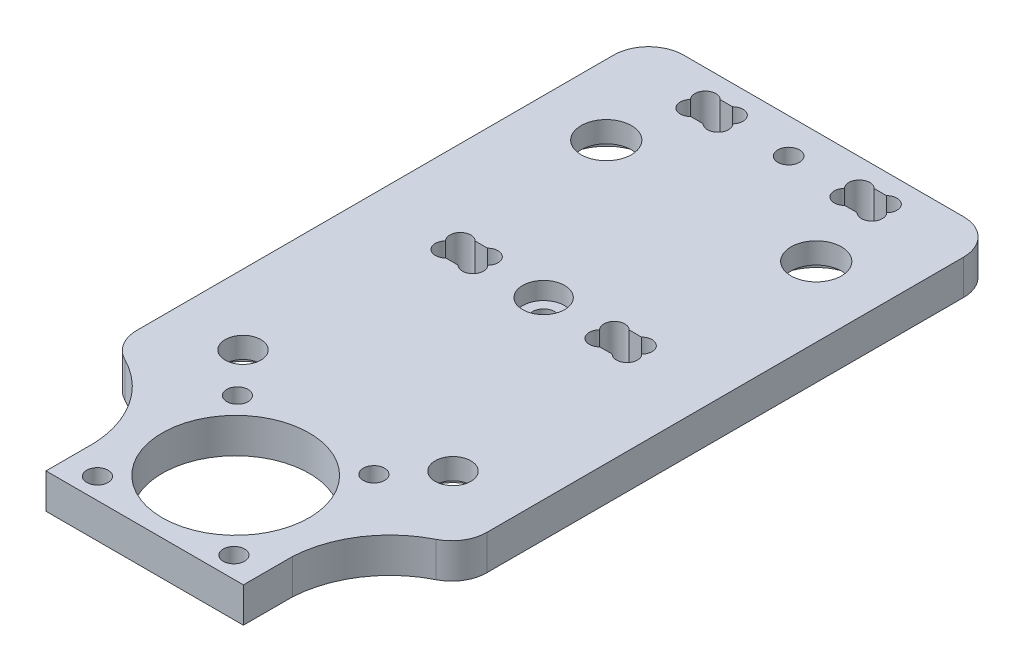
SolidWorks part; units mm, degrees
ref_plane "Alzado" through (0, 0, 0) normal (0, 0, 1) x (1, 0, 0)
ref_plane "Planta" through (0, 0, 0) normal (0, 1, 0) x (1, 0, 0)
ref_plane "Vista lateral" through (0, 0, 0) normal (1, 0, 0) x (0, 0, -1)
sketch "Croquis1" plane through (0, 0, 0) normal (0, 1, 0) x (1, 0, 0)
  line L0 (0, -36.0891) -> (0, 0) construction
  line L1 (-25, -48.5) -> (25, -48.5)
  line L2 (-25, -48.5) -> (-25, 48.5)
  line L3 (-25, 48.5) -> (25, 48.5)
  line L4 (25, -48.5) -> (25, 48.5)
  line L5 (-25, -48.5) -> (25, 48.5) construction
  line L6 (-25, 48.5) -> (25, -48.5) construction
  point P0 (0, 0)
  dimension "D2" = 50
  dimension "D1" = 97
extrude "Saliente-Extruir1" add sketch "Croquis1" along normal blind 5
sketch "Croquis3" plane through (0, 5, 0) normal (0, 1, 0) x (1, 0, 0)
  line L0 (0, -48.5) -> (0, 48.5) construction
  line L1 (-25, -48.5) -> (25, -48.5) construction
  line L2 (-14.1, -41.5) -> (-14.1, -48.5)
  line L3 (25, -48.5) -> (14.1, -48.5)
  line L4 (-25, -28.05) -> (-25, -48.5)
  line L5 (25, -28.05) -> (25, -48.5)
  line L6 (-25, -48.5) -> (-14.1, -48.5)
  line L7 (14.1, -41.5) -> (14.1, -48.5)
  line L10 (25, 48.5) -> (-25, 48.5) construction
  arc A0 (14.1, -41.5) -> (25, -28.05) centre (28.8286, -42.2945) cw
  arc A1 (-14.1, -41.5) -> (-25, -28.05) centre (-28.8286, -42.2945) ccw
  dimension "D1" = 7
  dimension "D3" = 29.5
  dimension "D2" = 20.45
  dimension "D4" = 14.1
extrude "Cortar-Extruir1" cut sketch "Croquis3" against normal through all
sketch "Croquis2" plane through (0, 5, 0) normal (0, 1, 0) x (1, 0, 0)
  line L0 (0, 6.5) -> (0, 48.5) construction
  line L1 (-15, -19.45) -> (15, -19.45) construction
  line L2 (-15, -19.45) -> (-15, 32.45) construction
  line L3 (-15, 32.45) -> (15, 32.45) construction
  line L4 (15, -19.45) -> (15, 32.45) construction
  line L5 (-15, -19.45) -> (15, 32.45) construction
  line L6 (-15, 32.45) -> (15, -19.45) construction
  line L7 (25, 48.5) -> (-25, 48.5) construction
  circle A0 centre (-15, 32.45) radius 3.6
  circle A1 centre (15, 32.45) radius 3.6
  circle A2 centre (15, -19.45) radius 2.55
  circle A3 centre (-15, -19.45) radius 2.55
  point P0 (0, 6.5)
  dimension "D3" = 7.2
  dimension "D5" = 5.1
  dimension "D1" = 30
  dimension "D2" = 51.9
  dimension "D4" = 42
extrude "Cortar-Extruir2" cut sketch "Croquis2" against normal through all
sketch "Croquis4" plane through (0, 0, 0) normal (0, -1, 0) x (1, 0, 0)
  circle A0 centre (15, -32.45) radius 6
  circle A1 centre (-15, -32.45) radius 6
  circle A2 centre (-15, 19.45) radius 5.05
  circle A3 centre (15, 19.45) radius 5.05
  dimension "D1" = 12
  dimension "D2" = 10.1
extrude "Cortar-Extruir3" cut sketch "Croquis4" against normal blind 2
fillet "Redondeo1" radius 5 4 edges at (-25, 2.5, 28.05) (-25, 2.5, -48.5) (25, 2.5, -48.5) (25, 2.5, 28.05)
sketch "Croquis5" plane through (0, 5, 0) normal (0, 1, 0) x (1, 0, 0)
  line L1 (-25, 45.6) -> (25, 45.6) construction
  line L2 (-25, 45.6) -> (-25, 41.4) construction
  line L3 (-25, 41.4) -> (25, 41.4) construction
  line L4 (25, 45.6) -> (25, 41.4) construction
  line L5 (-25, 43.5) -> (-25, -24.6276) construction
  line L6 (25, -24.6276) -> (25, 43.5) construction
  line L7 (20, 48.5) -> (-20, 48.5) construction
  line L8 (-11, 45.6) -> (-11, 41.4) construction
  line L9 (-14, 45.6) -> (-8, 45.6)
  line L10 (-14, 45.6) -> (-14, 41.4)
  line L11 (-14, 41.4) -> (-8, 41.4)
  line L12 (-8, 45.6) -> (-8, 41.4)
  line L13 (8, 45.6) -> (14, 45.6)
  line L14 (8, 45.6) -> (8, 41.4)
  line L15 (8, 41.4) -> (14, 41.4)
  line L16 (14, 45.6) -> (14, 41.4)
  line L17 (11, 45.6) -> (11, 41.4) construction
  line L18 (-11, 43.5) -> (-25, 43.5) construction
  line L19 (11, 43.5) -> (25, 43.5) construction
  line L20 (0, 45.6) -> (0, 41.4) construction
  circle A0 centre (0, 43.5) radius 1.55
  dimension "D5" = 3.1
  dimension "D1" = 4.2
  dimension "D2" = 2.9
  dimension "D3" = 6
  dimension "D4" = 14
extrude "Cortar-Extruir4" cut sketch "Croquis5" against normal through all
ref_plane "Plano1" through (0, 0, -43.5) normal (0, 0, 1) x (1, 0, 0)
ref_plane "Plano2" through (0, 0, -8.5) normal (0, 0, -1) x (-1, 0, 0)
ref_plane "Plano3" through (0, 0, -26) normal (0, 0, 1) x (1, 0, 0)
ref_plane "Plano5" through (0, 2.5, 0) normal (0, -1, 0) x (-1, 0, 0)
sketch "Croquis8" plane through (0, 5, 0) normal (0, 1, 0) x (1, 0, 0)
  line L0 (0, 43.5) -> (0, 51.5203) construction
  line L1 (-11.8787, 45.6) -> (-10.1213, 45.6)
  line L2 (-8, 45.6) -> (-14, 45.6) construction
  line L3 (-10.1213, 41.4) -> (-11.8787, 41.4)
  line L4 (-14, 45.6) -> (-14, 41.4) construction
  line L5 (-14, 45.6) -> (-12.5, 44.1) construction
  line L6 (-14, 41.4) -> (-8, 41.4) construction
  line L7 (14, 45.6) -> (12.5, 44.1) construction
  line L8 (10.1213, 41.4) -> (11.8787, 41.4)
  line L9 (11.8787, 45.6) -> (10.1213, 45.6)
  arc A0 (-11.8787, 45.6) -> (-14.0209, 43.5) centre (-12.9393, 44.5393) ccw
  arc A1 (-7.9791, 43.5) -> (-10.1213, 45.6) centre (-9.0607, 44.5393) ccw
  arc A2 (-10.1213, 41.4) -> (-7.9791, 43.5) centre (-9.0607, 42.4607) ccw
  arc A3 (-14.0209, 43.5) -> (-11.8787, 41.4) centre (-12.9393, 42.4607) ccw
  circle A4 centre (-12.5, 44.1) radius 1.5 construction
  circle A5 centre (12.5, 44.1) radius 1.5 construction
  arc A6 (14.0209, 43.5) -> (11.8787, 41.4) centre (12.9393, 42.4607) cw
  arc A7 (10.1213, 41.4) -> (7.9791, 43.5) centre (9.0607, 42.4607) cw
  arc A8 (7.9791, 43.5) -> (10.1213, 45.6) centre (9.0607, 44.5393) cw
  arc A9 (11.8787, 45.6) -> (14.0209, 43.5) centre (12.9393, 44.5393) cw
  dimension "D1" = 3
extrude "Cortar-Extruir6" cut sketch "Croquis8" against normal through all
mirror "Simetría1" about plane through (0, 0, -26) normal (0, 0, 1) of "Cortar-Extruir6", "Cortar-Extruir4"
sketch "Croquis14" plane through (0, 5, 0) normal (0, 1, 0) x (1, 0, 0)
  circle A0 centre (0, 8.5) radius 3
  dimension "D1" = 6
extrude "Cortar-Extruir9" cut sketch "Croquis14" against normal blind 2.5
sketch "Croquis17" plane through (0, 0, 0) normal (0, 1, 0) x (1, 0, 0)
  line L1 (-40, -60) -> (40, -60)
  line L2 (-40, -60) -> (-40, 60)
  line L3 (-40, 60) -> (40, 60)
  line L4 (40, -60) -> (40, 60)
  point P0 (0, 0)
  dimension "D1" = 120
  dimension "D2" = 80
sketch "Croquis18" plane through (0, 5, 0) normal (0, 1, 0) x (1, 0, 0)
  line L0 (-14.1, -48.5) -> (14.1, -48.5) construction
  line L1 (0, -35.5) -> (0, -48.5) construction
  line L3 (9.75, -45.5) -> (-9.75, -45.5) construction
  line L4 (9.75, -45.5) -> (9.75, -25.5) construction
  line L5 (9.75, -25.5) -> (-9.75, -25.5) construction
  line L6 (-9.75, -45.5) -> (-9.75, -25.5) construction
  line L7 (9.75, -45.5) -> (-9.75, -25.5) construction
  line L8 (9.75, -25.5) -> (-9.75, -45.5) construction
  circle A0 centre (0, -35.5) radius 10.5
  circle A2 centre (9.75, -45.5) radius 1.525
  circle A3 centre (-9.75, -45.5) radius 1.525
  circle A4 centre (9.75, -25.5) radius 1.525
  circle A5 centre (-9.75, -25.5) radius 1.525
  dimension "D2" = 21
  dimension "D5" = 3.05
  dimension "D1" = 13
  dimension "D3" = 20
  dimension "D4" = 19.5
extrude "Cortar-Extruir10" cut sketch "Croquis18" against normal through all
